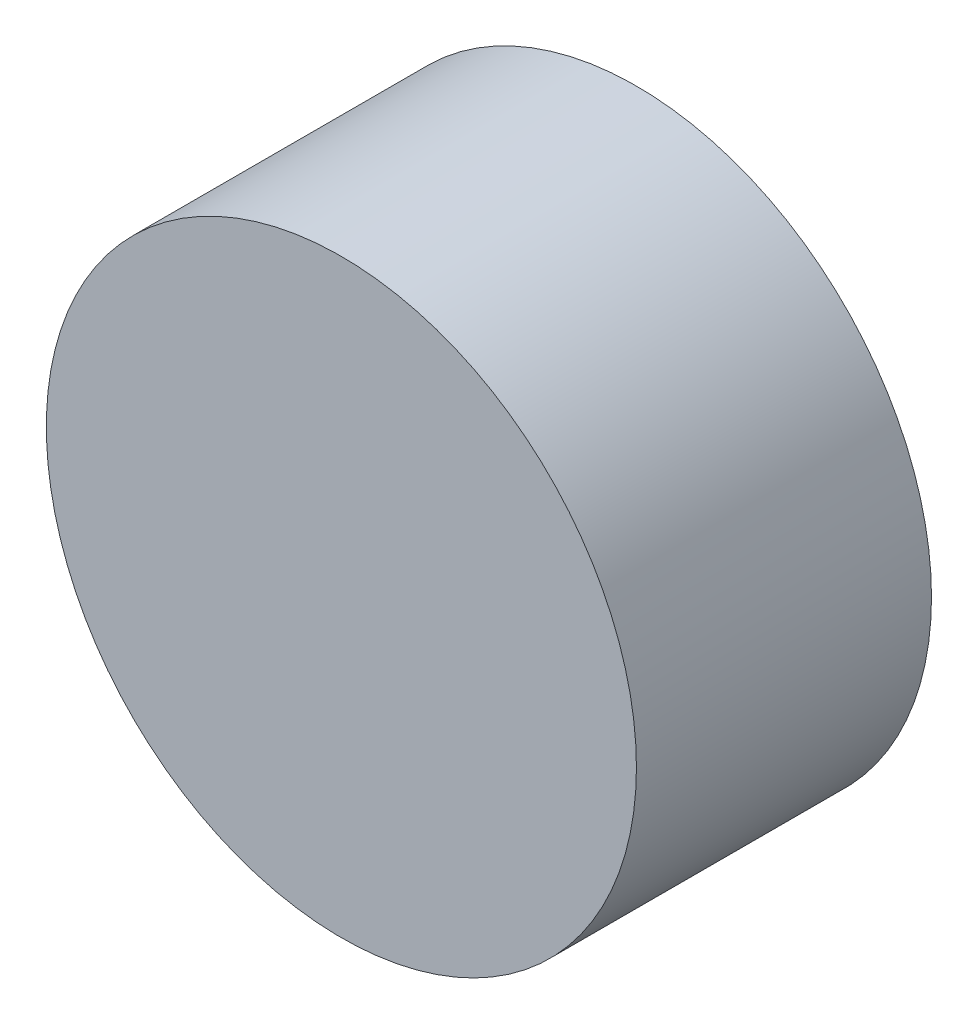
SolidWorks part; units mm, degrees
ref_plane "Front Plane" through (0, 0, 0) normal (0, 0, 1) x (1, 0, 0)
ref_plane "Top Plane" through (0, 0, 0) normal (0, 1, 0) x (1, 0, 0)
ref_plane "Right Plane" through (0, 0, 0) normal (1, 0, 0) x (0, 0, -1)
sketch "Sketch1" plane through (0, 0, 0) normal (0, 0, 1) x (1, 0, 0)
  line L0 (-0.9904, 11.7566) -> (0.9904, 11.7566)
  line L1 (0, -55) -> (0, 55) construction
  line L2 (0.9904, 11.7566) -> (2.0096, 9.796)
  line L3 (-0.9904, 11.7566) -> (-2.0096, 9.796)
  circle A0 centre (0, 0) radius 10
  point P10 (0, 11.7566)
extrude "Boss-Extrude1" add sketch "Sketch1" along normal blind 10 contours A0
